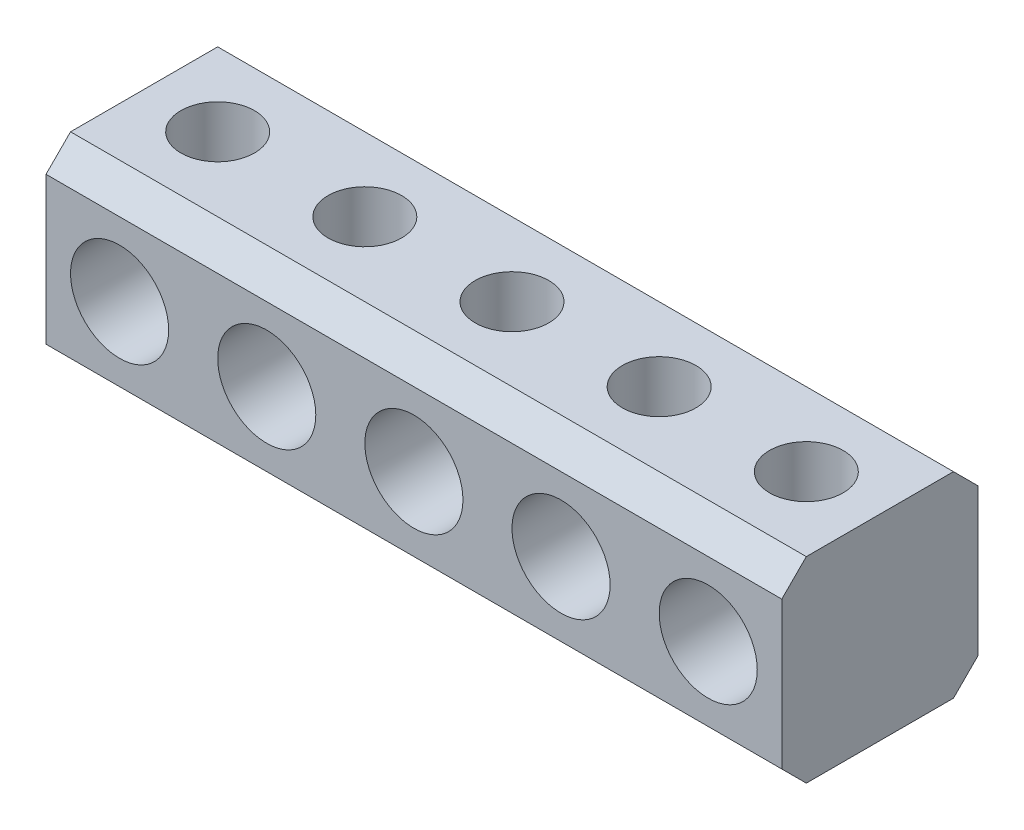
SolidWorks part; units mm, degrees
ref_plane "Alzado" through (0, 0, 0) normal (0, 0, 1) x (1, 0, 0)
ref_plane "Planta" through (0, 0, 0) normal (0, 1, 0) x (1, 0, 0)
ref_plane "Vista lateral" through (0, 0, 0) normal (1, 0, 0) x (0, 0, -1)
sketch "Croquis1" plane through (0, 0, 0) normal (0, 1, 0) x (1, 0, 0)
  line L1 (-232.7087, 55.8573) -> (67.2913, 55.8573)
  line L2 (-232.7087, 55.8573) -> (-232.7087, -24.1427)
  line L3 (-232.7087, -24.1427) -> (67.2913, -24.1427)
  line L4 (67.2913, 55.8573) -> (67.2913, -24.1427)
  line L5 (-232.7087, 55.8573) -> (67.2913, -24.1427) construction
  line L6 (-232.7087, -24.1427) -> (67.2913, 55.8573) construction
  point P0 (-82.7087, 15.8573)
  dimension "D1" = 300
  dimension "D2" = 80
extrude "Saliente-Extruir1" add sketch "Croquis1" along normal blind 80
chamfer "Chaflán1" distance 10 angle 45 4 edges at (-82.7087, 80, -55.8573) (-82.7087, 0, -55.8573) (-82.7087, 0, 24.1427) (-82.7087, 80, 24.1427)
sketch "Croquis2" plane through (0, 0, 24.1427) normal (0, 0, 1) x (1, 0, 0)
  line L0 (-82.7087, 70) -> (-82.7087, -21.0565) construction
  line L1 (67.2913, 70) -> (-232.7087, 70) construction
  line L2 (-232.7087, 40) -> (67.2913, 40) construction
  line L3 (-232.7087, 70) -> (-232.7087, 10) construction
  line L4 (67.2913, 70) -> (67.2913, 10) construction
  circle A0 centre (-82.7087, 40) radius 20
  circle A1 centre (-142.7087, 40) radius 20
  circle A2 centre (-202.7087, 40) radius 20
  circle A3 centre (-22.7087, 40) radius 20
  circle A4 centre (37.2913, 40) radius 20
  dimension "D1" = 40
  dimension "D2" = 40
  dimension "D3" = 40
  dimension "D4" = 40
  dimension "D5" = 40
  dimension "D6" = 60
  dimension "D7" = 60
  dimension "D8" = 60
  dimension "D9" = 60
extrude "Cortar-Extruir1" cut sketch "Croquis2" against normal blind 40
sketch "Croquis3" plane through (0, 80, 0) normal (0, 1, 0) x (1, 0, 0)
  line L0 (-232.7087, 15.8573) -> (65.2581, 15.8573) construction
  line L1 (-232.7087, 45.8573) -> (-232.7087, -14.1427) construction
  line L2 (65.2581, 15.8573) -> (-232.7087, 15.8573) construction
  line L3 (-82.7087, 45.8573) -> (-82.7087, -14.1427) construction
  line L4 (67.2913, 45.8573) -> (-232.7087, 45.8573) construction
  line L5 (-232.7087, -14.1427) -> (67.2913, -14.1427) construction
  line L6 (-82.7087, -14.1427) -> (-82.7087, 45.8573) construction
  circle A0 centre (-82.7087, 15.8573) radius 15
  circle A1 centre (-22.7087, 15.8573) radius 15
  circle A2 centre (37.2913, 15.8573) radius 15
  circle A3 centre (-142.7087, 15.8573) radius 15
  circle A4 centre (-202.7087, 15.8573) radius 15
  dimension "D1" = 30
  dimension "D2" = 30
  dimension "D3" = 30
  dimension "D4" = 30
  dimension "D5" = 30
  dimension "D6" = 60
  dimension "D7" = 60
  dimension "D8" = 60
  dimension "D9" = 60
extrude "Cortar-Extruir2" cut sketch "Croquis3" against normal mid plane 200
